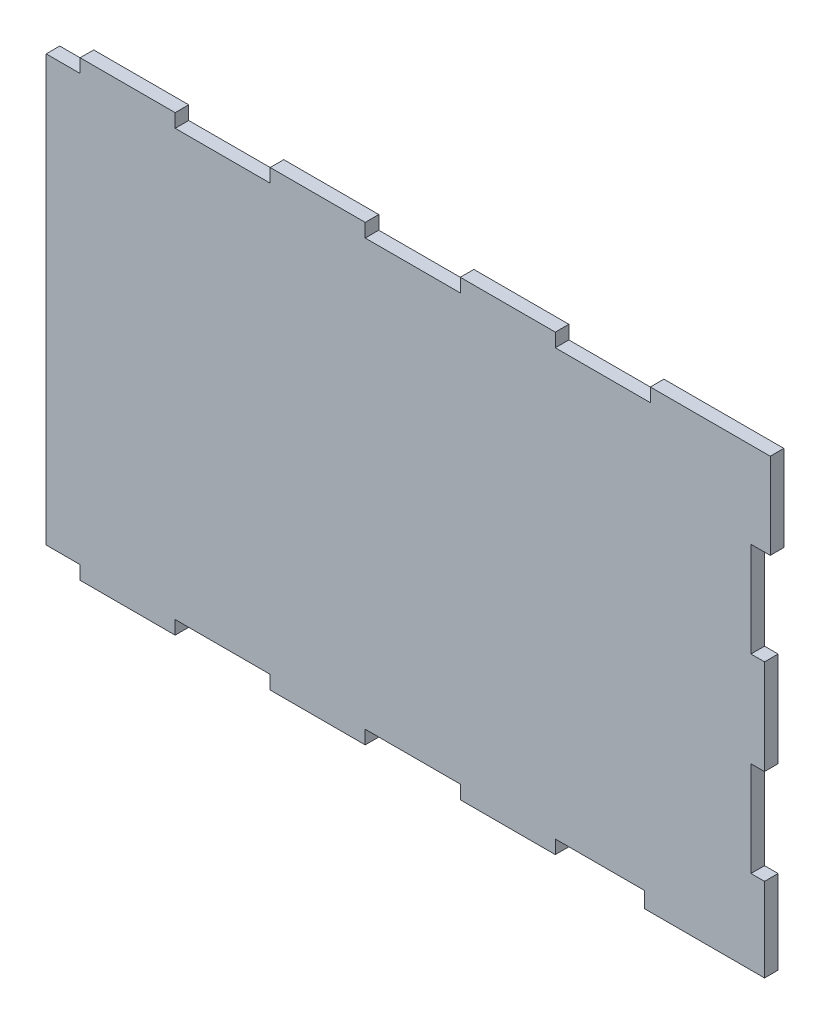
SolidWorks part; units mm, degrees
ref_plane "Alzado" through (0, 0, 0) normal (0, 0, 1) x (1, 0, 0)
ref_plane "Planta" through (0, 0, 0) normal (0, 1, 0) x (1, 0, 0)
ref_plane "Vista lateral" through (0, 0, 0) normal (1, 0, 0) x (0, 0, -1)
sketch "Croquis1" plane through (0, 0, 0) normal (0, 0, 1) x (1, 0, 0)
  line L0 (-99.3681, 50.2426) -> (-99.3681, 31.7426)
  line L1 (-99.3681, 31.7426) -> (-96.3681, 31.7426)
  line L2 (-96.3681, 31.7426) -> (-96.3681, 10.7426)
  line L3 (-96.3681, 10.7426) -> (-99.3681, 10.7426)
  line L4 (-99.3681, 10.7426) -> (-99.3681, -10.2574)
  line L5 (-99.3681, -10.2574) -> (-96.3681, -10.2574)
  line L6 (-96.3681, -10.2574) -> (-96.3681, -31.2574)
  line L7 (-96.3681, -31.2574) -> (-99.3681, -31.2574)
  line L8 (-99.3681, -31.2574) -> (-99.3681, -49.7574)
  line L9 (-99.3681, -49.7574) -> (-72.8681, -49.7574)
  line L10 (-72.8681, -49.7574) -> (-72.8681, -46.7574)
  line L11 (-72.8681, -46.7574) -> (-51.8681, -46.7574)
  line L12 (-51.8681, -46.7574) -> (-51.8681, -49.7574)
  line L13 (-51.8681, -49.7574) -> (-30.8681, -49.7574)
  line L14 (-30.8681, -49.7574) -> (-30.8681, -46.7574)
  line L15 (-30.8681, -46.7574) -> (-9.8681, -46.7574)
  line L16 (-9.8681, -46.7574) -> (-9.8681, -49.7574)
  line L17 (-9.8681, -49.7574) -> (11.1319, -49.7574)
  line L18 (11.1319, -49.7574) -> (11.1319, -46.7574)
  line L19 (11.1319, -46.7574) -> (32.1319, -46.7574)
  line L20 (32.1319, -46.7574) -> (32.1319, -49.7574)
  line L21 (32.1319, -49.7574) -> (53.1319, -49.7574)
  line L22 (53.1319, -49.7574) -> (53.1319, -46.7574)
  line L23 (53.1319, -46.7574) -> (72.8681, -46.7574)
  line L24 (72.8681, -46.7574) -> (72.8681, -50.2426)
  line L25 (72.8681, -50.2426) -> (93.8681, -50.2426)
  line L26 (93.8681, -50.2426) -> (99.3681, -50.2426)
  line L27 (99.3681, -50.2426) -> (99.3681, -31.7426)
  line L28 (99.3681, -31.7426) -> (96.3681, -31.7426)
  line L29 (96.3681, -31.7426) -> (96.3681, -10.7426)
  line L30 (96.3681, -10.7426) -> (99.3681, -10.7426)
  line L31 (99.3681, -10.7426) -> (99.3681, 10.2574)
  line L32 (99.3681, 10.2574) -> (96.3681, 10.2574)
  line L33 (96.3681, 10.2574) -> (96.3681, 31.2574)
  line L34 (96.3681, 31.2574) -> (100.6319, 31.2574)
  line L35 (100.6319, 31.2574) -> (100.6319, 50.2426)
  line L36 (100.6319, 50.2426) -> (74.1319, 50.2426)
  line L37 (74.1319, 50.2426) -> (74.1319, 47.2426)
  line L38 (74.1319, 47.2426) -> (53.1319, 47.2426)
  line L39 (53.1319, 47.2426) -> (53.1319, 50.2426)
  line L40 (53.1319, 50.2426) -> (32.1319, 50.2426)
  line L41 (32.1319, 50.2426) -> (32.1319, 47.2426)
  line L42 (32.1319, 47.2426) -> (11.1319, 47.2426)
  line L43 (11.1319, 47.2426) -> (11.1319, 50.2426)
  line L44 (11.1319, 50.2426) -> (-9.8681, 50.2426)
  line L45 (-9.8681, 50.2426) -> (-9.8681, 47.2426)
  line L46 (-9.8681, 47.2426) -> (-30.8681, 47.2426)
  line L47 (-30.8681, 47.2426) -> (-30.8681, 50.2426)
  line L48 (-30.8681, 50.2426) -> (-51.8681, 50.2426)
  line L49 (-51.8681, 50.2426) -> (-51.8681, 47.2426)
  line L50 (-51.8681, 47.2426) -> (-72.8681, 47.2426)
  line L51 (-72.8681, 47.2426) -> (-72.8681, 50.2426)
  line L52 (-72.8681, 50.2426) -> (-93.8681, 50.2426)
  line L53 (-93.8681, 50.2426) -> (-99.3681, 50.2426)
  line L54 (-99.3681, 50.2426) -> (99.3681, -50.2426) construction
  line L55 (-99.3681, -49.7574) -> (100.6319, 50.2426) construction
  point P54 (0, 0)
  dimension "D1" = 200
  dimension "D2" = 100
extrude "Saliente-Extruir1" add sketch "Croquis1" along normal blind 3 contours L2 L3 L4 L5 L6 L7 L8 L9 L10 L11 L12 L13 L14 L15 L16 L17 L18 L19 L20 L21 L22 L23 L24 L25 L26 L27 L28 L29 L30 L31 L32 L33 L34 L35 L36 L37 L38 L39 L40 L41 L42 L43 L44 L45 L46 L47 L48 L49 L50 L51 L52 L53 L0 L1
sketch "Croquis2" plane through (0, 0, 3) normal (0, 0, 1) x (1, 0, 0)
  line L5 (-99.3681, 50.2426) -> (-59.3681, 50.2426)
  line L6 (-99.3681, 50.2426) -> (-99.3681, -49.7574)
  line L7 (-99.3681, -49.7574) -> (-59.3681, -49.7574)
  line L8 (-59.3681, 50.2426) -> (-59.3681, -49.7574)
  line L56 (-99.3681, 31.7426) -> (-96.3681, 31.7426)
  line L57 (-96.3681, 31.7426) -> (-96.3681, 10.7426)
  line L58 (-96.3681, 10.7426) -> (-99.3681, 10.7426)
  line L59 (-99.3681, 10.7426) -> (-99.3681, -10.2574)
  line L60 (-99.3681, -10.2574) -> (-96.3681, -10.2574)
  line L61 (-96.3681, -10.2574) -> (-96.3681, -31.2574)
  line L62 (-96.3681, -31.2574) -> (-99.3681, -31.2574)
  line L63 (-99.3681, -31.2574) -> (-99.3681, -49.7574)
  line L64 (-99.3681, -49.7574) -> (-72.8681, -49.7574)
  line L65 (-72.8681, -49.7574) -> (-72.8681, -46.7574)
  line L66 (-72.8681, -46.7574) -> (-51.8681, -46.7574)
  line L67 (-51.8681, -46.7574) -> (-51.8681, -49.7574)
  line L68 (-51.8681, -49.7574) -> (-30.8681, -49.7574)
  line L69 (-30.8681, -49.7574) -> (-30.8681, -46.7574)
  line L70 (-30.8681, -46.7574) -> (-9.8681, -46.7574)
  line L71 (-9.8681, -46.7574) -> (-9.8681, -49.7574)
  line L72 (-9.8681, -49.7574) -> (11.1319, -49.7574)
  line L73 (11.1319, -49.7574) -> (11.1319, -46.7574)
  line L74 (11.1319, -46.7574) -> (32.1319, -46.7574)
  line L75 (32.1319, -46.7574) -> (32.1319, -49.7574)
  line L76 (32.1319, -49.7574) -> (53.1319, -49.7574)
  line L77 (53.1319, -49.7574) -> (53.1319, -46.7574)
  line L78 (53.1319, -46.7574) -> (72.8681, -46.7574)
  line L79 (72.8681, -46.7574) -> (72.8681, -50.2426)
  line L80 (72.8681, -50.2426) -> (99.3681, -50.2426)
  line L81 (99.3681, -50.2426) -> (99.3681, -31.7426)
  line L82 (99.3681, -31.7426) -> (96.3681, -31.7426)
  line L83 (96.3681, -31.7426) -> (96.3681, -10.7426)
  line L84 (96.3681, -10.7426) -> (99.3681, -10.7426)
  line L85 (99.3681, -10.7426) -> (99.3681, 10.2574)
  line L86 (99.3681, 10.2574) -> (96.3681, 10.2574)
  line L87 (96.3681, 10.2574) -> (96.3681, 31.2574)
  line L88 (96.3681, 31.2574) -> (100.6319, 31.2574)
  line L89 (100.6319, 31.2574) -> (100.6319, 50.2426)
  line L90 (100.6319, 50.2426) -> (74.1319, 50.2426)
  line L91 (74.1319, 50.2426) -> (74.1319, 47.2426)
  line L92 (74.1319, 47.2426) -> (53.1319, 47.2426)
  line L93 (53.1319, 47.2426) -> (53.1319, 50.2426)
  line L94 (53.1319, 50.2426) -> (32.1319, 50.2426)
  line L95 (32.1319, 50.2426) -> (32.1319, 47.2426)
  line L96 (32.1319, 47.2426) -> (11.1319, 47.2426)
  line L97 (11.1319, 47.2426) -> (11.1319, 50.2426)
  line L98 (11.1319, 50.2426) -> (-9.8681, 50.2426)
  line L99 (-9.8681, 50.2426) -> (-9.8681, 47.2426)
  line L100 (-9.8681, 47.2426) -> (-30.8681, 47.2426)
  line L101 (-30.8681, 47.2426) -> (-30.8681, 50.2426)
  line L102 (-30.8681, 50.2426) -> (-51.8681, 50.2426)
  line L103 (-51.8681, 50.2426) -> (-51.8681, 47.2426)
  line L104 (-51.8681, 47.2426) -> (-72.8681, 47.2426)
  line L105 (-72.8681, 47.2426) -> (-72.8681, 50.2426)
  line L106 (-72.8681, 50.2426) -> (-99.3681, 50.2426)
  line L107 (-99.3681, 50.2426) -> (-99.3681, 31.7426)
  line L108 (-99.3681, 31.7426) -> (-96.3681, 31.7426)
  line L109 (-96.3681, 31.7426) -> (-96.3681, 10.7426)
  line L110 (-96.3681, 10.7426) -> (-99.3681, 10.7426)
  line L111 (-99.3681, 10.7426) -> (-99.3681, -10.2574)
  line L112 (-99.3681, -10.2574) -> (-96.3681, -10.2574)
  line L113 (-96.3681, -10.2574) -> (-96.3681, -31.2574)
  line L114 (-96.3681, -31.2574) -> (-99.3681, -31.2574)
  line L115 (-99.3681, -31.2574) -> (-99.3681, -49.7574)
  line L116 (-99.3681, -49.7574) -> (-72.8681, -49.7574)
  line L117 (-72.8681, -49.7574) -> (-72.8681, -46.7574)
  line L118 (-72.8681, -46.7574) -> (-51.8681, -46.7574)
  line L119 (-51.8681, -46.7574) -> (-51.8681, -49.7574)
  line L120 (-51.8681, -49.7574) -> (-30.8681, -49.7574)
  line L121 (-30.8681, -49.7574) -> (-30.8681, -46.7574)
  line L122 (-30.8681, -46.7574) -> (-9.8681, -46.7574)
  line L123 (-9.8681, -46.7574) -> (-9.8681, -49.7574)
  line L124 (-9.8681, -49.7574) -> (11.1319, -49.7574)
  line L125 (11.1319, -49.7574) -> (11.1319, -46.7574)
  line L126 (11.1319, -46.7574) -> (32.1319, -46.7574)
  line L127 (32.1319, -46.7574) -> (32.1319, -49.7574)
  line L128 (32.1319, -49.7574) -> (53.1319, -49.7574)
  line L129 (53.1319, -49.7574) -> (53.1319, -46.7574)
  line L130 (53.1319, -46.7574) -> (72.8681, -46.7574)
  line L131 (72.8681, -46.7574) -> (72.8681, -50.2426)
  line L132 (72.8681, -50.2426) -> (99.3681, -50.2426)
  line L133 (99.3681, -50.2426) -> (99.3681, -31.7426)
  line L134 (99.3681, -31.7426) -> (96.3681, -31.7426)
  line L135 (96.3681, -31.7426) -> (96.3681, -10.7426)
  line L136 (96.3681, -10.7426) -> (99.3681, -10.7426)
  line L137 (99.3681, -10.7426) -> (99.3681, 10.2574)
  line L138 (99.3681, 10.2574) -> (96.3681, 10.2574)
  line L139 (96.3681, 10.2574) -> (96.3681, 31.2574)
  line L140 (96.3681, 31.2574) -> (100.6319, 31.2574)
  line L141 (100.6319, 31.2574) -> (100.6319, 50.2426)
  line L142 (100.6319, 50.2426) -> (74.1319, 50.2426)
  line L143 (74.1319, 50.2426) -> (74.1319, 47.2426)
  line L144 (74.1319, 47.2426) -> (53.1319, 47.2426)
  line L145 (53.1319, 47.2426) -> (53.1319, 50.2426)
  line L146 (53.1319, 50.2426) -> (32.1319, 50.2426)
  line L147 (32.1319, 50.2426) -> (32.1319, 47.2426)
  line L148 (32.1319, 47.2426) -> (11.1319, 47.2426)
  line L149 (11.1319, 47.2426) -> (11.1319, 50.2426)
  line L150 (11.1319, 50.2426) -> (-9.8681, 50.2426)
  line L151 (-9.8681, 50.2426) -> (-9.8681, 47.2426)
  line L152 (-9.8681, 47.2426) -> (-30.8681, 47.2426)
  line L153 (-30.8681, 47.2426) -> (-30.8681, 50.2426)
  line L154 (-30.8681, 50.2426) -> (-51.8681, 50.2426)
  line L155 (-51.8681, 50.2426) -> (-51.8681, 47.2426)
  line L156 (-51.8681, 47.2426) -> (-72.8681, 47.2426)
  line L157 (-72.8681, 47.2426) -> (-72.8681, 50.2426)
  line L158 (-72.8681, 50.2426) -> (-99.3681, 50.2426)
  line L159 (-99.3681, 50.2426) -> (-99.3681, 31.7426)
  dimension "D1" = 0
  dimension "D2" = 100
  dimension "D3" = 40
extrude "Cortar-Extruir3" cut sketch "Croquis2" against normal blind 10 contours L156 L157 L5 L6 L108 L109 L110 L112 L113 L114 L7 L117 L118 L8
